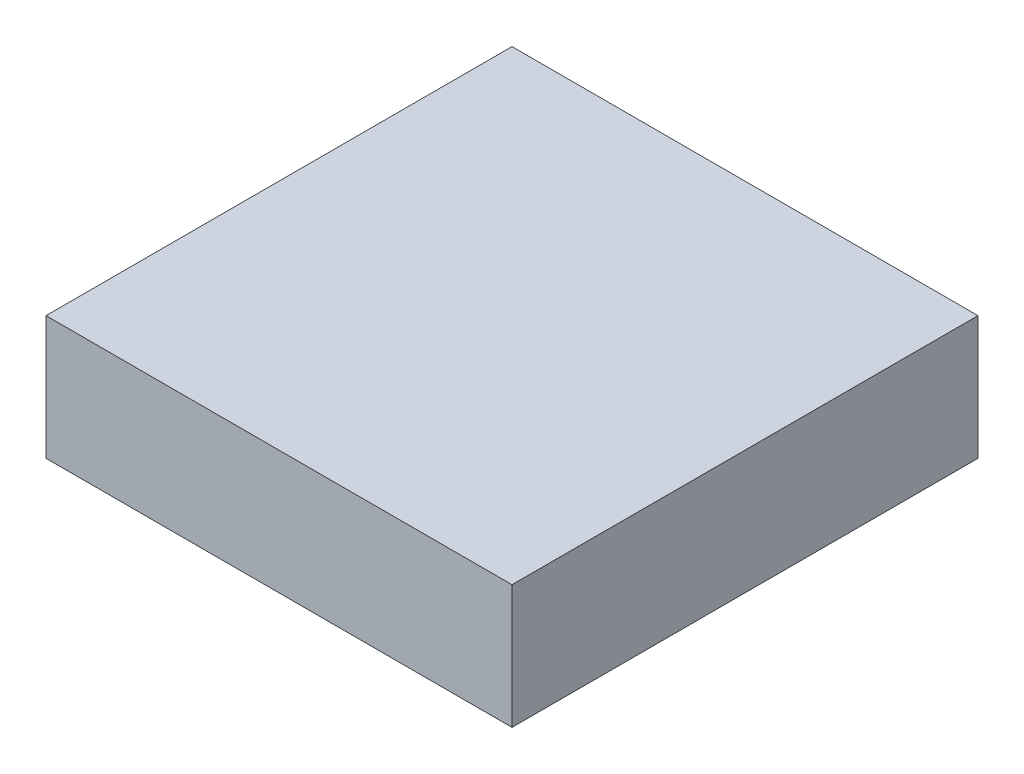
SolidWorks part; units mm, degrees
material "Cast Carbon Steel"
ref_plane "Front" through (0, 0, 0) normal (0, 0, 1) x (1, 0, 0)
ref_plane "Top" through (0, 0, 0) normal (0, 1, 0) x (1, 0, 0)
ref_plane "Right" through (0, 0, 0) normal (1, 0, 0) x (0, 0, -1)
sketch "Sketch1" plane through (0, 0, 0) normal (0, 1, 0) x (1, 0, 0)
  line L0 (-25, 25) -> (25, -25) construction
  line L1 (-25, 25) -> (25, 25)
  line L2 (-25, 25) -> (-25, -25)
  line L3 (-25, -25) -> (25, -25)
  line L4 (25, 25) -> (25, -25)
  point P4 (0, 0)
  dimension "D1" = 50
extrude "Extrude1" add sketch "Sketch1" along normal mid plane 13.26
